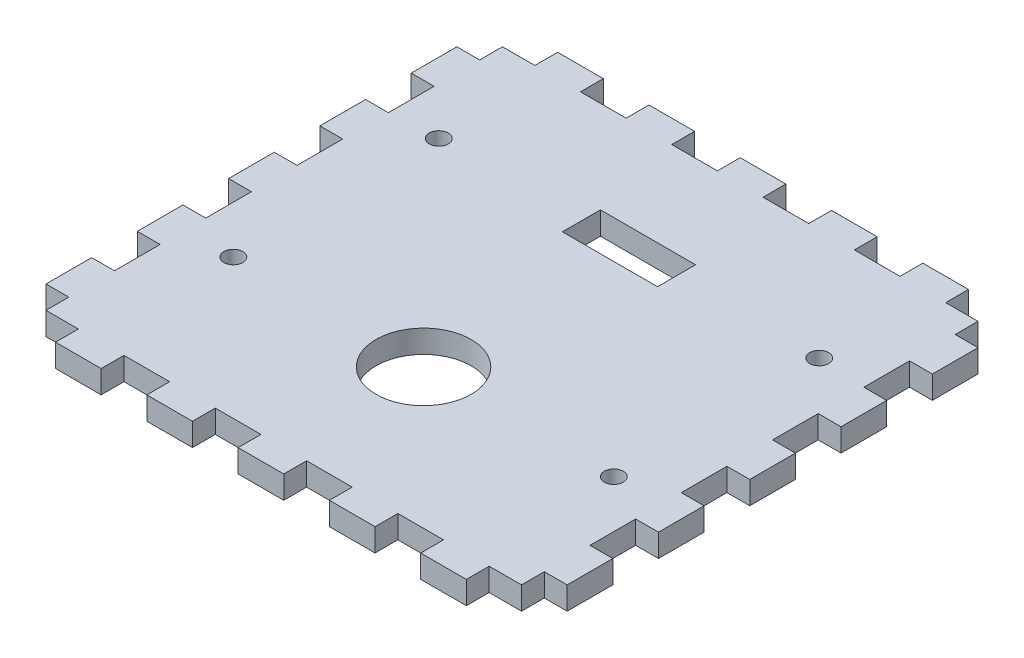
SolidWorks part; units mm, degrees
ref_plane "Front Plane" through (0, 0, 0) normal (0, 0, 1) x (1, 0, 0)
ref_plane "Top Plane" through (0, 0, 0) normal (0, 1, 0) x (1, 0, 0)
ref_plane "Right Plane" through (0, 0, 0) normal (1, 0, 0) x (0, 0, -1)
sketch "Sketch1" plane through (0, 0, 0) normal (0, 1, 0) x (1, 0, 0)
  line L0 (2.5, 38.5) -> (2.5, 60) construction
  line L1 (-62.5, -60) -> (62.5, -60)
  line L2 (-62.5, -60) -> (-62.5, 60)
  line L3 (-62.5, 60) -> (62.5, 60)
  line L4 (62.5, -60) -> (62.5, 60)
  line L5 (-62.5, -60) -> (62.5, 60) construction
  line L6 (-62.5, 60) -> (62.5, -60) construction
  line L7 (-37.5, -38.5) -> (2.5, -38.5)
  line L8 (-37.5, -38.5) -> (-37.5, 38.5)
  line L9 (-37.5, 38.5) -> (2.5, 38.5)
  line L10 (2.5, -38.5) -> (2.5, 38.5)
  line L11 (-37.5, -38.5) -> (2.5, 38.5) construction
  line L12 (-37.5, 38.5) -> (2.5, -38.5) construction
  line L13 (2.5, -38.5) -> (2.5, -60) construction
  line L14 (-37.5, 38.5) -> (-62.5, 38.5) construction
  line L15 (32.5, -36) -> (32.5, -21) construction
  line L16 (2.5, -38.5) -> (32.5, -38.5) construction
  line L17 (32.5, -21) -> (32.5, -6) construction
  line L18 (32.5, -6) -> (32.5, 9) construction
  line L19 (32.5, -38.5) -> (62.5, -38.5) construction
  line L20 (-54, 66) -> (-54, 60)
  line L21 (-62.5, 54) -> (-68.5, 54)
  line L22 (-54, 66) -> (-42, 66)
  line L23 (-42, 66) -> (-42, 60)
  line L24 (-18, 66) -> (-18, 60)
  line L25 (-30, 66) -> (-30, 60)
  line L26 (-30, 66) -> (-18, 66)
  line L27 (6, 66) -> (6, 60)
  line L28 (-6, 66) -> (-6, 60)
  line L29 (-6, 66) -> (6, 66)
  line L30 (30, 66) -> (30, 60)
  line L31 (18, 66) -> (18, 60)
  line L32 (18, 66) -> (30, 66)
  line L33 (54, 66) -> (54, 60)
  line L34 (42, 66) -> (42, 60)
  line L35 (42, 66) -> (54, 66)
  line L36 (-68.5, 54) -> (-68.5, 42)
  line L37 (-68.5, 42) -> (-62.5, 42)
  line L38 (-62.5, 30) -> (-68.5, 30)
  line L39 (-68.5, 30) -> (-68.5, 18)
  line L40 (-68.5, 18) -> (-62.5, 18)
  line L41 (-62.5, 6) -> (-68.5, 6)
  line L42 (-68.5, 6) -> (-68.5, -6)
  line L43 (-68.5, -6) -> (-62.5, -6)
  line L44 (-62.5, -18) -> (-68.5, -18)
  line L45 (-68.5, -18) -> (-68.5, -30)
  line L46 (-68.5, -30) -> (-62.5, -30)
  line L47 (-62.5, -42) -> (-68.5, -42)
  line L48 (-68.5, -42) -> (-68.5, -54)
  line L49 (-68.5, -54) -> (-62.5, -54)
  line L51 (0, -55) -> (0, 55) construction
  line L52 (68.5, -54) -> (62.5, -54)
  line L53 (68.5, -42) -> (68.5, -54)
  line L54 (62.5, -42) -> (68.5, -42)
  line L55 (68.5, -30) -> (62.5, -30)
  line L56 (68.5, -18) -> (68.5, -30)
  line L57 (62.5, -18) -> (68.5, -18)
  line L58 (68.5, -6) -> (62.5, -6)
  line L59 (68.5, 6) -> (68.5, -6)
  line L60 (62.5, 6) -> (68.5, 6)
  line L61 (68.5, 18) -> (62.5, 18)
  line L62 (68.5, 30) -> (68.5, 18)
  line L63 (62.5, 30) -> (68.5, 30)
  line L64 (68.5, 42) -> (62.5, 42)
  line L65 (68.5, 54) -> (68.5, 42)
  line L66 (-55, 0) -> (55, 0) construction
  line L67 (42, -66) -> (54, -66)
  line L68 (42, -66) -> (42, -60)
  line L69 (54, -66) -> (54, -60)
  line L70 (18, -66) -> (30, -66)
  line L71 (18, -66) -> (18, -60)
  line L72 (30, -66) -> (30, -60)
  line L73 (-6, -66) -> (6, -66)
  line L74 (-6, -66) -> (-6, -60)
  line L75 (6, -66) -> (6, -60)
  line L76 (-30, -66) -> (-18, -66)
  line L77 (-30, -66) -> (-30, -60)
  line L78 (-18, -66) -> (-18, -60)
  line L79 (-42, -66) -> (-42, -60)
  line L80 (-54, -66) -> (-42, -66)
  line L81 (-54, -66) -> (-54, -60)
  line L82 (62.5, 54) -> (68.5, 54)
  circle A0 centre (32.5, 9) radius 2.5
  circle A1 centre (32.5, -6) radius 2.5
  circle A2 centre (32.5, -21) radius 2.5
  circle A3 centre (32.5, -36) radius 2.5
  point P0 (0, 0)
  point P6 (-17.5, 0)
  dimension "D7" = 6
  dimension "D8" = 12
  dimension "D1" = 125
  dimension "D2" = 5
  dimension "D4" = 40
  dimension "D5" = 25
  dimension "D10" = 8.5
  dimension "D12" = 12
  dimension "D13" = 6
  dimension "D14" = 6
  dimension "D11" = 5
extrude "Boss-Extrude2" add sketch "Sketch1" along normal blind 6 contours L1 L4 L3 L2 A3 A2 A1 | L39 L40 L2 L38 | L36 L37 L2 L21 | L45 L46 L2 L44 | L42 L43 L2 L41 | L48 L49 L2 L47 | L81 L80 L79 L1 | L76 L78 L1 L77 | L73 L75 L1 L74 | L70 L72 L1 L71 | L67 L69 L1 L68 | L54 L4 L52 L53 | L57 L4 L55 L56 | L60 L4 L58 L59 | L63 L4 L61 L62 | L82 L4 L64 L65 | L35 L34 L3 L33 | L32 L31 L3 L30 | L29 L28 L3 L27 | L23 L22 L20 L3 | L26 L25 L3 L24 | L7 L10 L9 L8 | A0 | A1 | A3 | A2
sketch "Sketch2" plane through (0, 6, 0) normal (0, 1, 0) x (1, 0, 0)
  line L0 (-12.5, 30.75) -> (-62.5, 30.75)
  line L1 (-12.5, 25.75) -> (12.5, 25.75)
  line L2 (-12.5, 25.75) -> (-12.5, 35.75)
  line L3 (-12.5, 35.75) -> (12.5, 35.75)
  line L4 (12.5, 25.75) -> (12.5, 35.75)
  line L5 (-12.5, 25.75) -> (12.5, 35.75) construction
  line L6 (-12.5, 35.75) -> (12.5, 25.75) construction
  line L7 (-62.5, 30) -> (-62.5, 42) construction
  line L8 (0, 35.75) -> (0, 66)
  line L9 (-6, 66) -> (6, 66) construction
  line L10 (0, -66) -> (0, -35.75)
  line L11 (-6, -66) -> (6, -66) construction
  line L12 (12.5, 30.75) -> (62.5, 30.75)
  line L13 (62.5, 30) -> (62.5, 42) construction
  circle A0 centre (0, -23.25) radius 12.5
  circle A1 centre (-50, 30.75) radius 2.5
  circle A2 centre (50, 30.75) radius 2.5
  circle A3 centre (50, -23.25) radius 2.5
  circle A4 centre (-50, -23.25) radius 2.5
  point P5 (0, 30.75)
  point P26 (0, 0)
  dimension "D1" = 25
  dimension "D5" = 5
  dimension "D6" = 37.5
  dimension "D2" = 25
  dimension "D3" = 10
  dimension "D4" = 54
  dimension "D7" = 2
  dimension "D8" = 2
extrude "Cut-Extrude2" cut sketch "Sketch2" against normal blind 6 contours A4 | A0 | A3 | A1 | L1 L4 L3 L2 | A2
